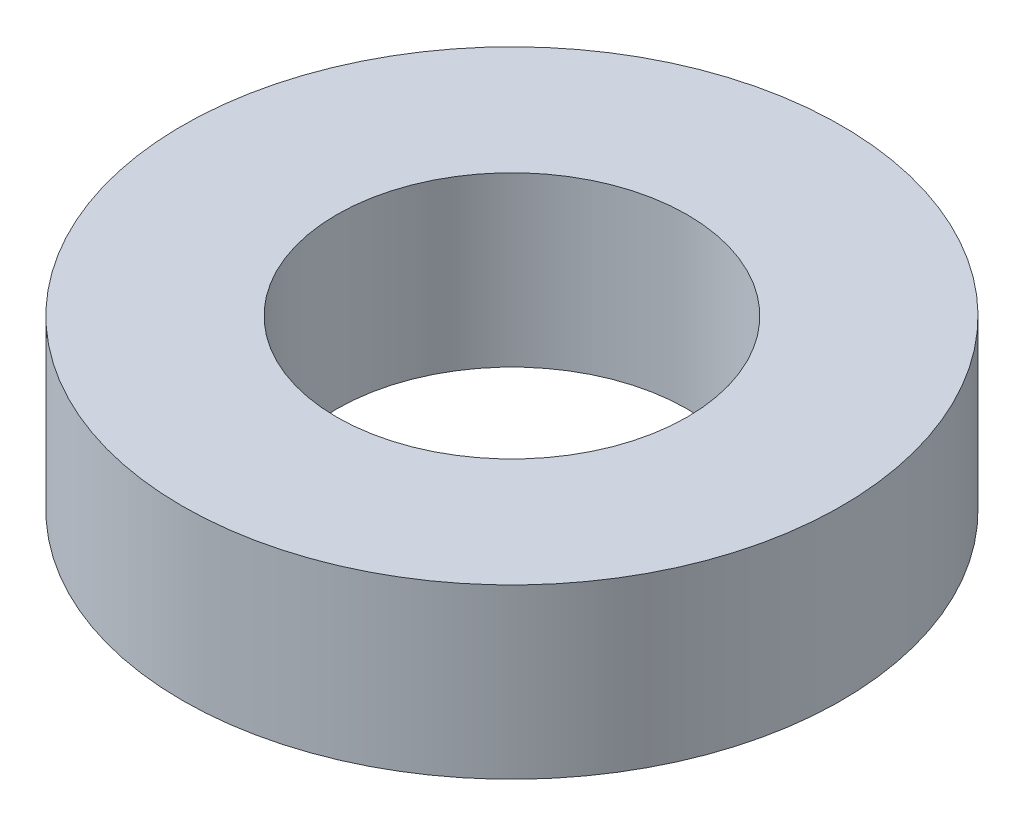
SolidWorks part; units mm, degrees
ref_plane "Front" through (0, 0, 0) normal (0, 0, 1) x (1, 0, 0)
ref_plane "Top" through (0, 0, 0) normal (0, 1, 0) x (1, 0, 0)
ref_plane "Right" through (0, 0, 0) normal (1, 0, 0) x (0, 0, -1)
sketch "Sketch1" plane through (0, 0, 0) normal (0, 1, 0) x (1, 0, 0)
  circle A0 centre (0, 0) radius 23.5
  circle A1 centre (0, 0) radius 12.5
  dimension "D1" = 47
  dimension "D2" = 25
extrude "Boss-Extrude1" add sketch "Sketch1" along normal blind 12
